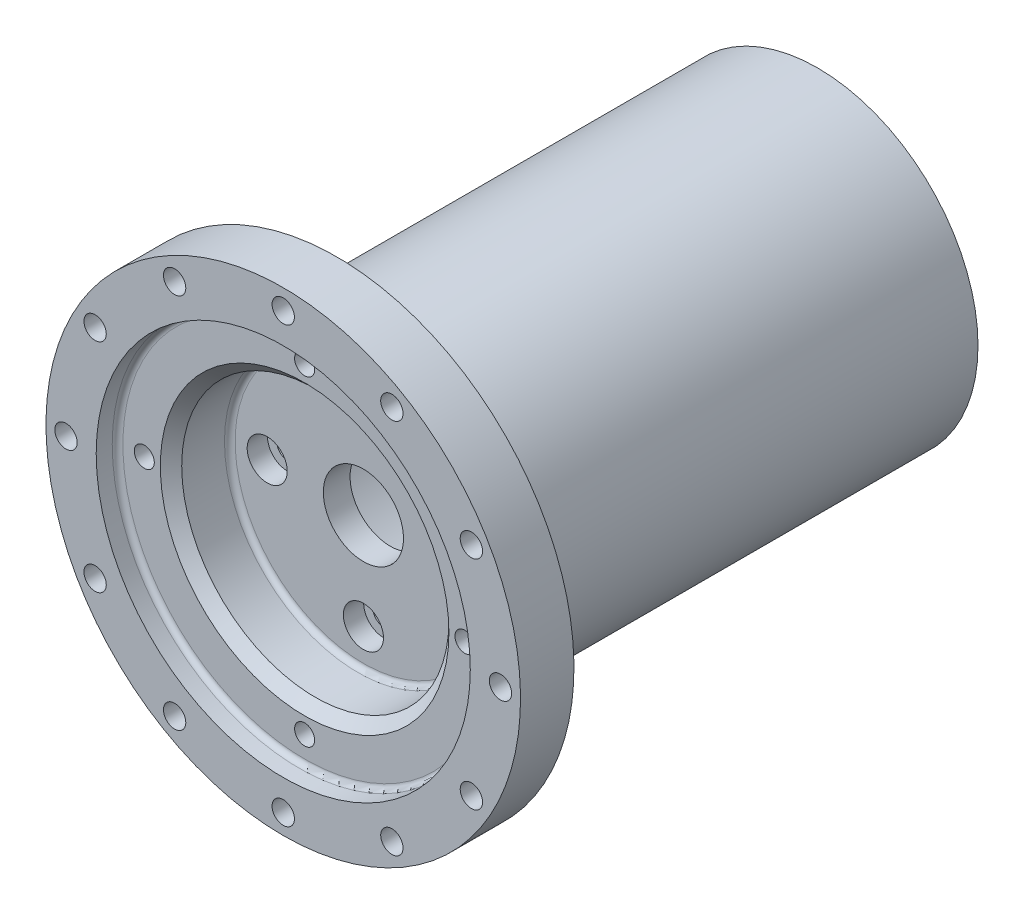
SolidWorks part; units mm, degrees
material "6061 Alloy"
ref_plane "Front Plane" through (0, 0, 0) normal (0, 0, 1) x (1, 0, 0)
ref_plane "Top Plane" through (0, 0, 0) normal (0, 1, 0) x (1, 0, 0)
ref_plane "Right Plane" through (0, 0, 0) normal (1, 0, 0) x (0, 0, -1)
sketch "Sketch1" plane through (0, 0, 0) normal (1, 0, 0) x (0, 0, -1)
  line L0 (-63.5, 0) -> (63.5, 0) construction
  line L2 (-63.5, 0) -> (63.5, 0)
  line L3 (63.5, 0) -> (63.5, 38.1)
  line L4 (63.5, 38.1) -> (-50.8, 38.1)
  line L5 (-50.8, 38.1) -> (-50.8, 56.388)
  line L6 (-50.8, 56.388) -> (-63.5, 56.388)
  line L8 (-63.5, 56.388) -> (-63.5, 0)
  point P3 (0, 0)
  dimension "D1" = 12.7
  dimension "D2" = 127
  dimension "D3" = 38.1
  dimension "D4" = 56.388
revolve "Revolve1" add sketch "Sketch1" angle 360 about L0
sketch "Sketch2" plane through (0, 0, -63.5) normal (0, 0, -1) x (-1, 0, 0)
  circle A1 centre (0, 0) radius 31.75
  dimension "D1" = 63.5
extrude "Cut-Extrude1" cut sketch "Sketch2" against normal blind 101.6
sketch "Sketch3" plane through (0, 0, 63.5) normal (0, 0, 1) x (1, 0, 0)
  circle A0 centre (0, 0) radius 31.75
  dimension "D1" = 63.5
extrude "Cut-Extrude2" cut sketch "Sketch3" against normal blind 19.05
sketch "Sketch4" plane through (0, 0, 44.45) normal (0, 0, 1) x (1, 0, 0)
  circle A0 centre (0, 0) radius 9.525
  dimension "D1" = 19.05
extrude "Cut-Extrude3" cut sketch "Sketch4" against normal through all
sketch "Sketch5" plane through (0, 0, 63.5) normal (0, 0, 1) x (1, 0, 0)
  circle A0 centre (0, 0) radius 44.45
  dimension "D1" = 88.9
extrude "Cut-Extrude4" cut sketch "Sketch5" against normal blind 5.08
fillet "Fillet1" radius 1.27 3 edges at (0, 31.75, 38.1) (31.75, 0, 44.45) (44.45, 0, 58.42)
fillet "Fillet2" radius 6.35 1 edges at (0, -38.1, 50.8)
chamfer "Chamfer1" distance 2.54 angle 45 1 edges at (31.75, 0, 58.42)
hole_wizard "CBORE for #10 Socket Head Cap Screw1" positions "Sketch6" profile "Sketch7" counterbore size "#10" standard "ANSI Inch" end condition through all
sketch "Sketch6" plane through (0, 0, 44.45) normal (0, 0, 1) x (1, 0, 0)
  circle A0 centre (0, 0) radius 22.86
  point P0 (0, 22.86)
  point P2 (22.86, 0)
  point P4 (0, -22.86)
  point P6 (-22.86, 0)
  dimension "D1" = 45.72
sketch "Sketch7" plane through (0, 22.86, 44.45) normal (1, 0, 0) x (0, -1, 0)
  line L0 (0, 0) -> (0, 107.95)
  line L1 (0, 107.95) -> (2.5527, 107.95)
  line L3 (2.5527, 107.95) -> (2.5527, 4.826)
  line L4 (2.5527, 4.826) -> (4.7625, 4.826)
  line L5 (4.7625, 4.826) -> (4.7625, 0)
  line L7 (4.7625, 0) -> (0, 0)
  line L11 (0, -6.35) -> (0, 107.95) construction
  dimension "Thru Hole Dia." = 5.1054
  dimension "Thru Hole Depth" = 107.95
  dimension "C'Bore Dia." = 9.525
  dimension "C'Bore Depth" = 4.826
hole_wizard "3/16 (0.1875) Diameter Hole1" positions "Sketch9" profile "Sketch10" hole size "3/16" standard "ANSI Inch"
sketch "Sketch9" plane through (0, 0, 58.42) normal (0, 0, 1) x (1, 0, 0)
  point P0 (0, 38.1)
  point P10 (38.1, 0)
  point P11 (0, -38.1)
  point P12 (-38.1, 0)
  point P13 (0, 0)
  dimension "D1" = 38.1
  dimension "D2" = 4
sketch "Sketch10" plane through (0, 38.1, 58.42) normal (1, 0, 0) x (0, -1, 0)
  line L0 (0, 0) -> (0, 7.7808)
  line L1 (0, 7.7808) -> (2.3812, 6.35)
  line L2 (2.3812, 6.35) -> (2.3812, 0)
  line L5 (2.3812, 0) -> (0, 0)
  line L10 (0, 7.7808) -> (-2.3812, 6.35) construction
  line L11 (0, -6.35) -> (0, 107.95) construction
  dimension "Hole Dia." = 4.7625
  dimension "Hole Depth" = 6.35
  dimension "Drill Angle" = 118
hole_wizard "#4 (0.209) Diameter Hole1" positions "Sketch11" profile "Sketch12" hole size "#4" standard "ANSI Inch" end condition through all
sketch "Sketch11" plane through (0, 0, 63.5) normal (0, 0, 1) x (1, 0, 0)
  point P0 (0, 51.6255)
  point P11 (25.8128, 44.709)
  point P12 (44.709, 25.8128)
  point P13 (51.6255, 0)
  point P14 (44.709, -25.8127)
  point P15 (25.8128, -44.709)
  point P16 (0, -51.6255)
  point P17 (-25.8127, -44.709)
  point P18 (-44.709, -25.8128)
  point P19 (-51.6255, 0)
  point P20 (-44.709, 25.8127)
  point P21 (-25.8127, 44.709)
  point P22 (0, 0)
  dimension "D1" = 51.6255
  dimension "D2" = 12
sketch "Sketch12" plane through (0, 51.6255, 63.5) normal (1, 0, 0) x (0, -1, 0)
  line L0 (0, 0) -> (0, 127)
  line L1 (0, 127) -> (2.6543, 127)
  line L2 (2.6543, 127) -> (2.6543, 0)
  line L5 (2.6543, 0) -> (0, 0)
  line L11 (0, -6.35) -> (0, 107.95) construction
  dimension "Thru Hole Dia." = 5.3086
  dimension "Thru Hole Depth" = 127
